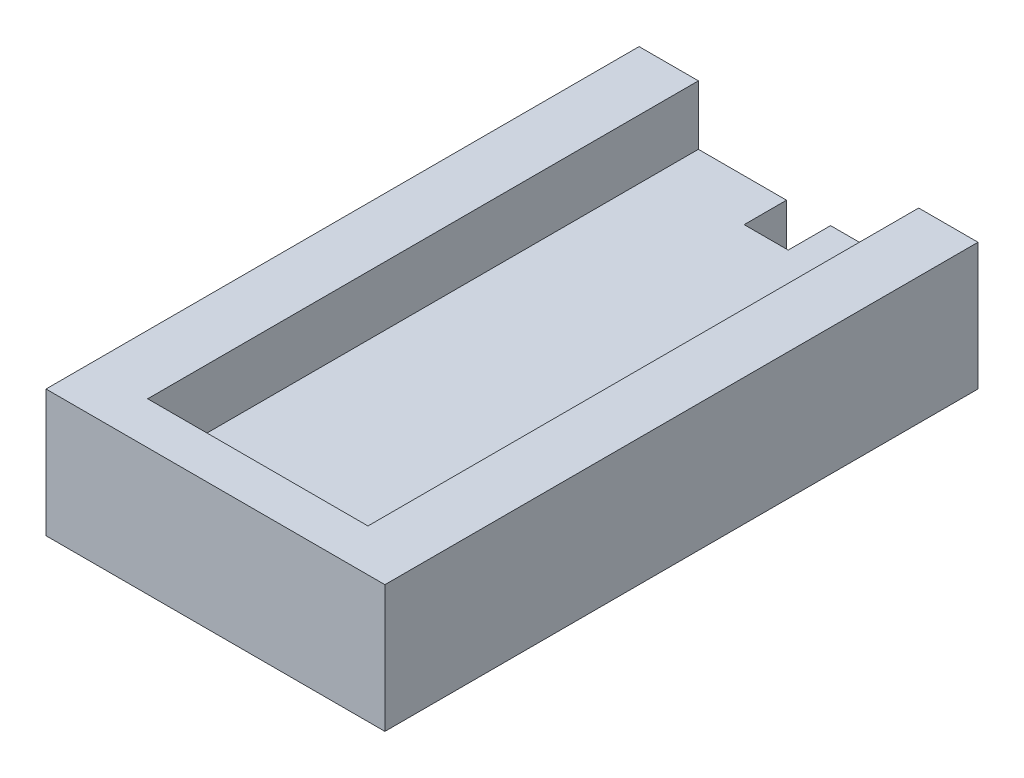
SolidWorks part; units mm, degrees
ref_plane "正面" through (0, 0, 0) normal (0, 0, 1) x (1, 0, 0)
ref_plane "平面" through (0, 0, 0) normal (0, 1, 0) x (1, 0, 0)
ref_plane "右側面" through (0, 0, 0) normal (1, 0, 0) x (0, 0, -1)
sketch "ｽｹｯﾁ1" plane through (0, 0, 0) normal (0, 0, 1) x (1, 0, 0)
  line L1 (-20, 15) -> (20, 15)
  line L2 (-20, 15) -> (-20, -15)
  line L3 (-20, -15) -> (20, -15)
  line L4 (20, 15) -> (20, -15)
  line L5 (-20, 15) -> (20, -15) construction
  line L6 (-20, -15) -> (20, 15) construction
  point P0 (0, 0)
  dimension "D1" = 30
  dimension "D2" = 40
extrude "ﾎﾞｽ - 押し出し1" add sketch "ｽｹｯﾁ1" along normal blind 70
sketch "ｽｹｯﾁ2" plane through (0, 0, 0) normal (0, 0, -1) x (-1, 0, 0)
  line L1 (13, 7) -> (-13, 7)
  line L2 (13, 7) -> (13, -7)
  line L3 (13, -7) -> (-13, -7)
  line L4 (-13, 7) -> (-13, -7)
  line L5 (13, 7) -> (-13, -7) construction
  line L6 (13, -7) -> (-13, 7) construction
  point P0 (0, 0)
  dimension "D1" = 26
  dimension "D2" = 14
extrude "ｶｯﾄ - 押し出し1" cut sketch "ｽｹｯﾁ2" against normal blind 65
sketch "ｽｹｯﾁ3" plane through (0, 7, 0) normal (0, -1, 0) x (-1, 0, 0)
  line L0 (13, 0) -> (-13, 0) construction
  line L1 (-2.6, 0) -> (2.6, 0)
  line L2 (-2.6, 0) -> (-2.6, -5)
  line L3 (-2.6, -5) -> (2.6, -5)
  line L4 (2.6, 0) -> (2.6, -5)
  line L5 (13, -65) -> (13, 0) construction
  dimension "D1" = 5
  dimension "D2" = 5.2
  dimension "D3" = 10.4
extrude "ｶｯﾄ - 押し出し2" cut sketch "ｽｹｯﾁ3" against normal blind 10
sketch "ｽｹｯﾁ4" plane through (0, -7, 0) normal (0, 1, 0) x (1, 0, 0)
  line L0 (13, 0) -> (-13, 0) construction
  line L1 (2.6, 0) -> (-2.6, 0)
  line L2 (2.6, 0) -> (2.6, -5)
  line L3 (2.6, -5) -> (-2.6, -5)
  line L4 (-2.6, 0) -> (-2.6, -5)
  line L5 (13, -65) -> (13, 0) construction
  dimension "D1" = 5.2
  dimension "D2" = 5
  dimension "D3" = 10.4
extrude "ｶｯﾄ - 押し出し3" cut sketch "ｽｹｯﾁ4" against normal blind 10
ref_plane "平面1" through (0, 0, 0) normal (0, -1, 0) x (-1, 0, 0)
other "ｻｰﾌｪｽ ｶｯﾄ1"
